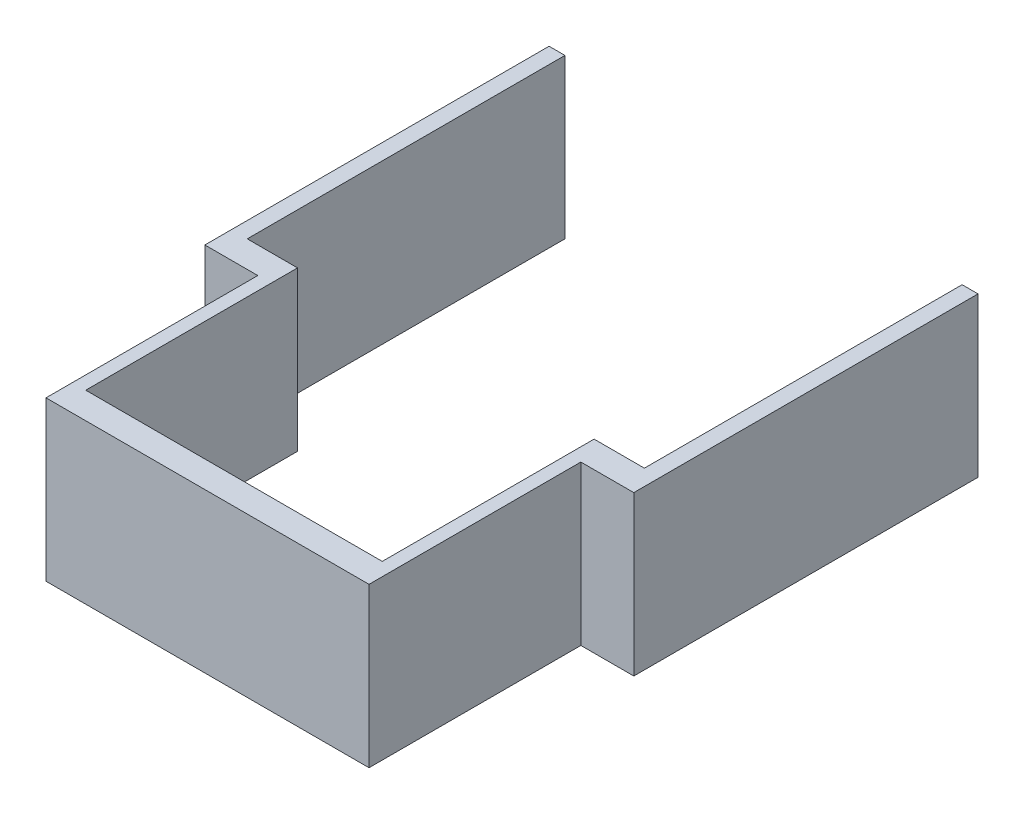
SolidWorks part; units mm, degrees
ref_plane "Plan de face" through (0, 0, 0) normal (0, 0, 1) x (1, 0, 0)
ref_plane "Plan de dessus" through (0, 0, 0) normal (0, 1, 0) x (1, 0, 0)
ref_plane "Plan de droite" through (0, 0, 0) normal (1, 0, 0) x (0, 0, -1)
sketch "Esquisse1" plane through (0, 0, 0) normal (0, 0, 1) x (1, 0, 0)
  line L1 (-32.9084, 15.6441) -> (28.0916, 15.6441)
  line L2 (-32.9084, 15.6441) -> (-32.9084, -14.3559)
  line L3 (-32.9084, -14.3559) -> (28.0916, -14.3559)
  line L4 (28.0916, 15.6441) -> (28.0916, -14.3559)
  dimension "D1" = 61
  dimension "D2" = 30
extrude "Boss.-Extru.1" add sketch "Esquisse1" along normal blind 45
sketch "Esquisse2" plane through (0, 0, 0) normal (0, 0, -1) x (-1, 0, 0)
  line L0 (32.9084, -14.3559) -> (-28.0916, -14.3559) construction
  line L5 (30.4084, -14.3559) -> (-25.5916, -14.3559)
  line L6 (30.4084, -14.3559) -> (30.4084, 15.6441)
  line L7 (30.4084, 15.6441) -> (-25.5916, 15.6441)
  line L8 (-25.5916, -14.3559) -> (-25.5916, 15.6441)
  line L9 (-28.0916, 15.6441) -> (32.9084, 15.6441) construction
  line L10 (-28.0916, -14.3559) -> (-28.0916, 15.6441) construction
  line L11 (32.9084, 15.6441) -> (32.9084, -14.3559) construction
  dimension "D1" = 56
  dimension "D2" = 2.5
  dimension "D3" = 2.5
extrude "Enlèv. mat.-Extru.1" cut sketch "Esquisse2" against normal blind 40
sketch "Esquisse3" plane through (28.0916, 0, 0) normal (1, 0, 0) x (0, 0, -1)
  line L0 (-45, -14.3559) -> (0, -14.3559) construction
  line L1 (-5, -14.3559) -> (0, -14.3559)
  line L2 (-5, -14.3559) -> (-5, 15.6441)
  line L3 (-5, 15.6441) -> (0, 15.6441)
  line L4 (0, -14.3559) -> (0, 15.6441)
  dimension "D1" = 5
extrude "Boss.-Extru.2" add sketch "Esquisse3" along normal blind 10
sketch "Esquisse4" plane through (-32.9084, 0, 0) normal (-1, 0, 0) x (0, 0, 1)
  line L0 (45, 15.6441) -> (0, 15.6441) construction
  line L1 (5, 15.6441) -> (0, 15.6441)
  line L2 (5, 15.6441) -> (5, -14.3559)
  line L3 (5, -14.3559) -> (0, -14.3559)
  line L4 (0, 15.6441) -> (0, -14.3559)
  dimension "D1" = 5
extrude "Boss.-Extru.3" add sketch "Esquisse4" along normal blind 10
sketch "Esquisse5" plane through (0, 0, 0) normal (0, 0, -1) x (-1, 0, 0)
  line L5 (-38.0916, 15.6441) -> (-25.5916, 15.6441) construction
  line L6 (-38.0916, -14.3559) -> (-35.0916, -14.3559)
  line L7 (-38.0916, -14.3559) -> (-38.0916, 15.6441)
  line L8 (-38.0916, 15.6441) -> (-35.0916, 15.6441)
  line L9 (-35.0916, -14.3559) -> (-35.0916, 15.6441)
  dimension "D1" = 3
extrude "Boss.-Extru.4" add sketch "Esquisse5" along normal blind 60
sketch "Esquisse6" plane through (0, 0, 0) normal (0, 0, -1) x (-1, 0, 0)
  line L0 (30.4084, 15.6441) -> (42.9084, 15.6441) construction
  line L1 (42.9084, -14.3559) -> (39.9084, -14.3559)
  line L2 (42.9084, -14.3559) -> (42.9084, 15.6441)
  line L3 (42.9084, 15.6441) -> (39.9084, 15.6441)
  line L4 (39.9084, -14.3559) -> (39.9084, 15.6441)
  dimension "D1" = 3
extrude "Boss.-Extru.5" add sketch "Esquisse6" along normal blind 60
